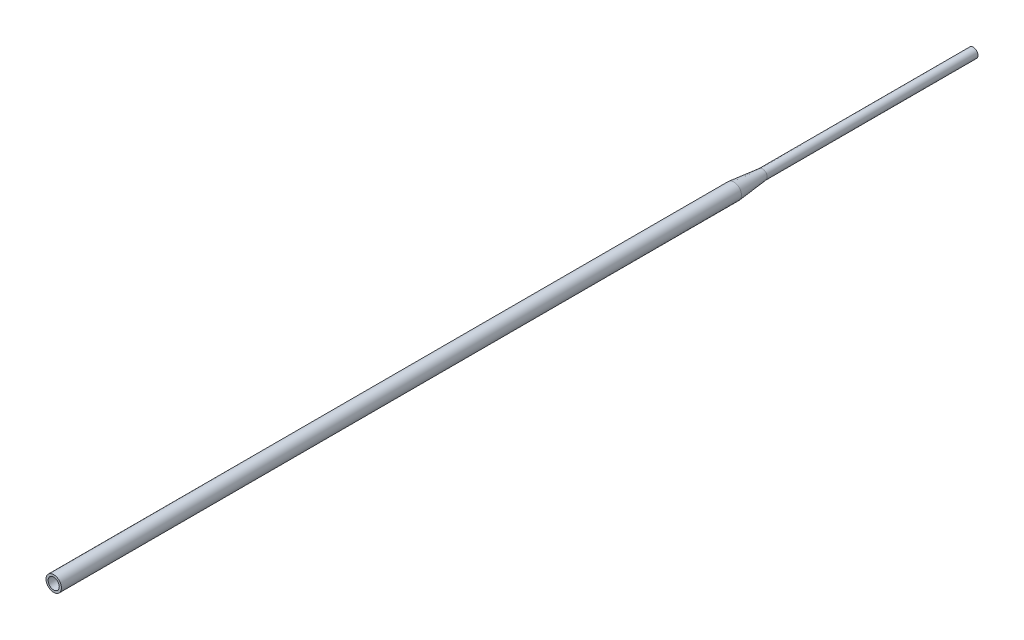
SolidWorks part; units mm, degrees
material "Hexcel AS4C (3000 Filaments)"
ref_plane "Top Plane" through (0, 0, 0) normal (0, 0, 1) x (1, 0, 0)
ref_plane "Front Plane" through (0, 0, 0) normal (0, 1, 0) x (1, 0, 0)
ref_plane "Right Plane" through (0, 0, 0) normal (1, 0, 0) x (0, 0, -1)
sketch "Sketch1" plane through (0, 0, 0) normal (0, 0, 1) x (1, 0, 0)
  circle A0 centre (0, 0) radius 4.699
  circle A1 centre (0, 0) radius 3.75
  dimension "D1" = 9.398
  dimension "D2" = 7.5
extrude "Boss-Extrude1" add sketch "Sketch1" along normal blind 215.9
ref_plane "Plane2" through (0, 0, 0) normal (0, 1, 0) x (1, 0, 0)
sketch "Sketch5" plane through (0, 0, 0) normal (0, 1, 0) x (1, 0, 0)
  line L0 (-4.699, -208.1237) -> (-7.62, -236.4485)
  line L1 (-4.699, 0) -> (-4.699, -215.9) construction
  line L2 (-7.62, -236.4485) -> (-5.08, -236.4485)
  line L3 (0, -215.9) -> (0, -244.0219) construction
  line L4 (-4.699, -215.9) -> (4.699, -215.9) construction
  line L5 (-5.08, -236.4485) -> (-5.08, -245.9)
  line L6 (-5.08, -245.9) -> (-3.58, -245.9)
  line L7 (-3.58, -245.9) -> (-3.58, -215.9)
  line L10 (-4.699, -215.9) -> (-4.699, -208.1237)
  line L11 (-3.75, -215.9) -> (3.75, -215.9) construction
  line L12 (-4.699, -215.9) -> (-3.58, -215.9)
  dimension "D1" = 1.5
  dimension "D2" = 5.08
  dimension "D3" = 7.62
  dimension "D5" = 30
revolve "Revolve1" add sketch "Sketch5" angle 360 about L3
sketch "Sketch6" plane through (0, 0, 236.4485) normal (0, 0, 1) x (1, 0, 0)
  circle A0 centre (0, 0) radius 7.62 construction
  circle A1 centre (0, 0) radius 7.62
  circle A2 centre (0, 0) radius 5.5
  dimension "D1" = 11
extrude "Boss-Extrude2" add sketch "Sketch6" along normal blind 671.6
